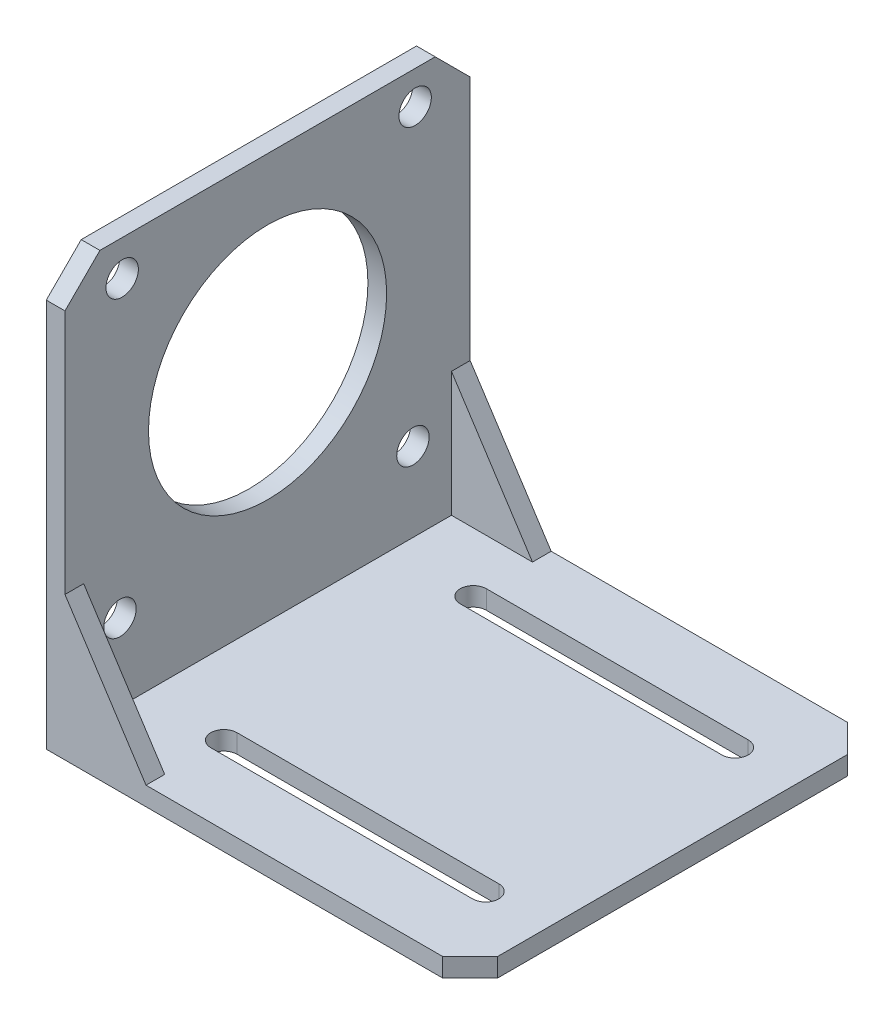
SolidWorks part; units mm, degrees
ref_plane "Front Plane" through (0, 0, 0) normal (0, 0, 1) x (1, 0, 0)
ref_plane "Top Plane" through (0, 0, 0) normal (0, 1, 0) x (1, 0, 0)
ref_plane "Right Plane" through (0, 0, 0) normal (1, 0, 0) x (0, 0, -1)
sketch "Sketch1" plane through (0, 0, 0) normal (0, 1, 0) x (1, 0, 0)
  line L1 (0, 0) -> (68, 0)
  line L2 (0, 0) -> (0, 65)
  line L3 (0, 65) -> (68, 65)
  line L4 (68, 0) -> (68, 65)
  dimension "D1" = 65
  dimension "D2" = 68
extrude "Boss-Extrude1" add sketch "Sketch1" along normal blind 68
sketch "Sketch2" plane through (0, 0, 0) normal (0, 0, 1) x (1, 0, 0)
  line L0 (0, 68) -> (3, 68)
  line L1 (0, 68) -> (68, 68) construction
  line L2 (3, 68) -> (3, 23)
  line L3 (3, 23) -> (16, 3)
  line L4 (16, 3) -> (68, 3)
  line L5 (68, 68) -> (68, 0) construction
  line L6 (68, 3) -> (68, 0)
  line L7 (68, 0) -> (0, 0)
  line L8 (0, 0) -> (0, 68)
  line L9 (3, 68) -> (68, 68)
  line L10 (68, 68) -> (68, 3)
  line L11 (16, 3) -> (3, 3)
  line L12 (3, 3) -> (3, 23)
  line M9 (68, 0) -> (68, 68)
  line M10 (68, 68) -> (0, 68)
  dimension "D1" = 3
  dimension "D2" = 3
  dimension "D3" = 13
  dimension "D4" = 20
extrude "Cut-Extrude1" cut sketch "Sketch2" against normal through all contours L3 L4 L2 M9 M10
sketch "Sketch3" plane through (68, 0, 0) normal (1, 0, 0) x (0, 0, -1)
  line L0 (65, 3) -> (0, 3) construction
  line L1 (3, 3) -> (62, 3)
  line L2 (3, 3) -> (3, 23)
  line L3 (3, 23) -> (62, 23)
  line L4 (62, 3) -> (62, 23)
  line L5 (65, 23) -> (0, 23) construction
  line L6 (0, 23) -> (0, 3) construction
  line L7 (65, 23) -> (65, 3) construction
  dimension "D1" = 3
  dimension "D2" = 3
extrude "Cut-Extrude2" cut sketch "Sketch3" against normal up to surface (65 mm away) up to face at (3, 45.5, -32.5)
sketch "Sketch4" plane through (3, 0, 0) normal (1, 0, 0) x (0, 0, -1)
  line L0 (0, 39) -> (65, 39) construction
  line L1 (0, 68) -> (0, 23) construction
  line L2 (65, 68) -> (65, 23) construction
  line L3 (65, 68) -> (0, 68) construction
  line L4 (32.5, 68) -> (32.5, 0) construction
  line L5 (0, 0) -> (65, 0) construction
  line L7 (56.1764, 62.6764) -> (8.8236, 15.3236) construction
  line L8 (9.1778, 62.3222) -> (55.8222, 15.6778) construction
  line L9 (0, 62.3958) -> (5.6042, 68)
  line L10 (59.3958, 68) -> (65, 62.3958)
  line L11 (0, 62.3958) -> (0, 68)
  line L12 (0, 68) -> (5.6042, 68)
  line L13 (59.3958, 68) -> (65, 68)
  line L14 (65, 68) -> (65, 62.3958)
  circle A0 centre (32.5, 39) radius 19.1
  circle A6 centre (55.8222, 15.6778) radius 2.6
  circle A7 centre (56.1764, 62.6764) radius 2.6
  circle A8 centre (9.1778, 62.3222) radius 2.6
  circle A9 centre (8.8236, 15.3236) radius 2.6
  point P10 (12.38, 59.12)
  point P11 (22.6005, 48.8995)
  point P12 (12.38, 18.88)
  point P13 (8.8236, 62.6764)
  point P21 (32.5, 39)
  point P46 (32.5, 39)
  dimension "D2" = 38.2
  dimension "D3" = 45
  dimension "D4" = 45
  dimension "D5" = 47
  dimension "D7" = 5.2
  dimension "D9" = 29
  dimension "D6" = 46.9987
  dimension "D10" = 45
extrude "Cut-Extrude3" cut sketch "Sketch4" against normal through all
sketch "Sketch5" plane through (0, 3, 0) normal (0, 1, 0) x (1, 0, 0)
  line L0 (16, 54.6) -> (58, 54.6)
  line L1 (16, 50.4) -> (58, 50.4)
  line L2 (68, 65) -> (68, 0) construction
  line L3 (68, 32.5) -> (0, 32.5) construction
  line L4 (0, 59.3958) -> (0, 5.6042) construction
  line L5 (63.5735, 65) -> (68, 60.5735)
  line L6 (16, 65) -> (68, 65) construction
  line L7 (68, 60.5735) -> (68, 65)
  line L8 (68, 65) -> (63.5735, 65)
  line L9 (63.5735, 0) -> (68, 4.4265)
  line L10 (16, 0) -> (68, 0) construction
  line L11 (68, 4.4265) -> (68, 0)
  line L12 (68, 0) -> (63.5735, 0)
  line L13 (16, 10.4) -> (58, 10.4)
  line L14 (16, 14.6) -> (58, 14.6)
  circle A0 centre (16, 52.5) radius 2.1
  circle A1 centre (58, 52.5) radius 2.1
  circle A2 centre (58, 12.5) radius 2.1
  circle A3 centre (16, 12.5) radius 2.1
  line M12 (16, 0) -> (68, 0)
  line M13 (68, 0) -> (68, 65)
  line M14 (68, 65) -> (16, 65)
  dimension "D1" = 42
  dimension "D3" = 45
  dimension "D4" = 4.2
  dimension "D2" = 10
  dimension "D5" = 40
  dimension "D6" = 40
extrude "Cut-Extrude4" cut sketch "Sketch5" against normal through all contours A1 L0 A0 L1 | A0 | A1 | L5 M14 M13 | L9 M12 M13 | A2 | L14 A3 L13 A2 | A3 L1
